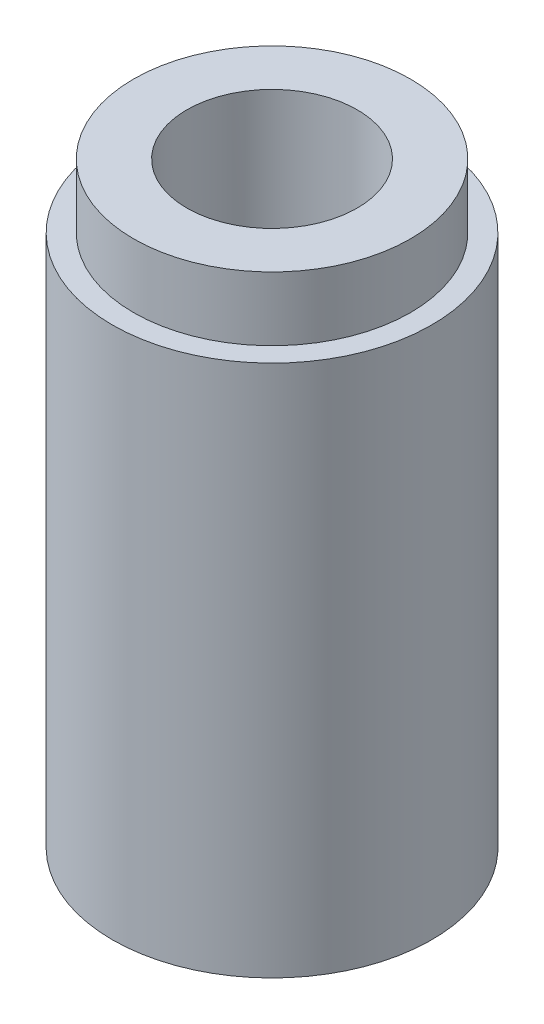
SolidWorks part; units mm, degrees
ref_plane "Front Plane" through (0, 0, 0) normal (0, 0, 1) x (1, 0, 0)
ref_plane "Top Plane" through (0, 0, 0) normal (0, 1, 0) x (1, 0, 0)
ref_plane "Right Plane" through (0, 0, 0) normal (1, 0, 0) x (0, 0, -1)
sketch "Sketch1" plane through (0, 0, 0) normal (0, 1, 0) x (1, 0, 0)
  circle A0 centre (0, 0) radius 7.5
  dimension "D1" = 15
extrude "Boss-Extrude1" add sketch "Sketch1" along normal blind 25
sketch "Sketch2" plane through (0, 25, 0) normal (0, 1, 0) x (1, 0, 0)
  circle A0 centre (0, 0) radius 6.5
  dimension "D1" = 13
extrude "Boss-Extrude2" add sketch "Sketch2" along normal blind 3
sketch "Sketch3" plane through (0, 0, 0) normal (0, -1, 0) x (1, 0, 0)
  circle A0 centre (0, 0) radius 5.1
  dimension "D1" = 10.2
extrude "Cut-Extrude1" cut sketch "Sketch3" against normal blind 7
sketch "Sketch4" plane through (0, 28, 0) normal (0, 1, 0) x (1, 0, 0)
  circle A0 centre (0, 0) radius 4
  dimension "D1" = 8
extrude "Cut-Extrude2" cut sketch "Sketch4" against normal through all
